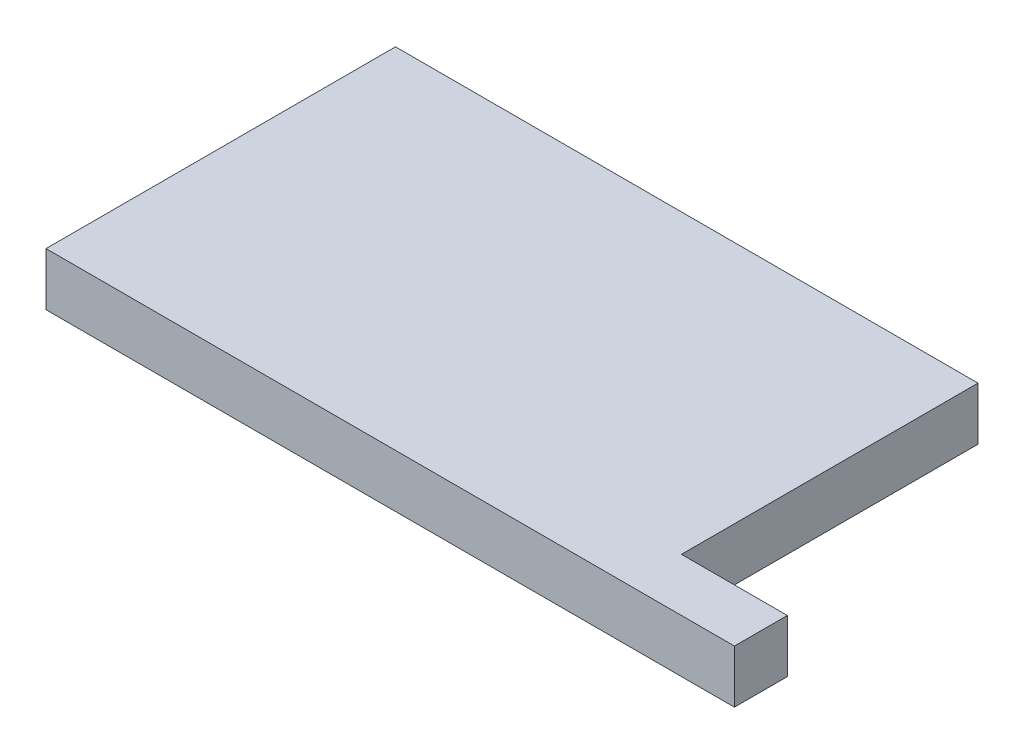
SolidWorks part; units mm, degrees
ref_plane "Front Plane" through (0, 0, 0) normal (0, 0, 1) x (1, 0, 0)
ref_plane "Top Plane" through (0, 0, 0) normal (0, 1, 0) x (1, 0, 0)
ref_plane "Right Plane" through (0, 0, 0) normal (1, 0, 0) x (0, 0, -1)
sketch "Sketch1" plane through (0, 0, 0) normal (0, 1, 0) x (1, 0, 0)
  line L1 (-27.5, -16.5) -> (27.5, -16.5)
  line L2 (-27.5, -16.5) -> (-27.5, 16.5)
  line L3 (-27.5, 16.5) -> (27.5, 16.5)
  line L4 (27.5, -16.5) -> (27.5, 16.5)
  line L5 (-27.5, -16.5) -> (27.5, 16.5) construction
  line L6 (-27.5, 16.5) -> (27.5, -16.5) construction
  line L7 (27.5, -16.5) -> (37.5, -16.5)
  line L8 (27.5, -16.5) -> (27.5, -11.5)
  line L9 (27.5, -11.5) -> (37.5, -11.5)
  line L10 (37.5, -16.5) -> (37.5, -11.5)
  point P0 (0, 0)
  dimension "D1" = 33
  dimension "55mm" = 55
  dimension "D2" = 10
  dimension "D3" = 5
extrude "Boss-Extrude1" add sketch "Sketch1" along normal mid plane 5 contours L1 L4 L3 L2 | L7 L10 L9 L4
